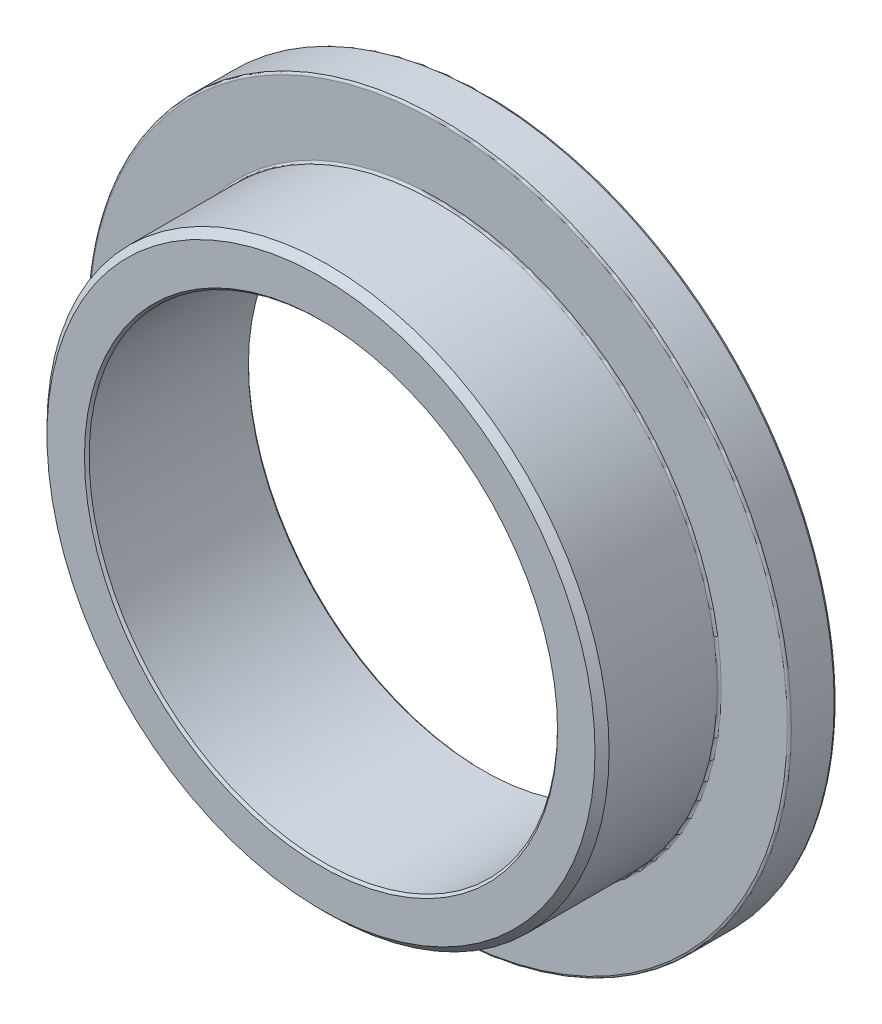
SolidWorks part; units mm, degrees
ref_plane "Front Plane" through (0, 0, 0) normal (0, 0, 1) x (1, 0, 0)
ref_plane "Top Plane" through (0, 0, 0) normal (0, 1, 0) x (1, 0, 0)
ref_plane "Right Plane" through (0, 0, 0) normal (1, 0, 0) x (0, 0, -1)
sketch "Sketch1" plane through (0, 0, 0) normal (0, 0, 1) x (1, 0, 0)
  circle A0 centre (0, 0) radius 5 construction
  circle A1 centre (0, 0) radius 6 construction
  circle A2 centre (0, 0) radius 7.5 construction
  point P5 (0, 7.5)
  dimension "ID" = 10
  dimension "OD" = 12
  dimension "Flange OD" = 15
sketch "Sketch2" plane through (0, 0, 0) normal (1, 0, 0) x (0, 0, -1)
  line L0 (-1.75, 0) -> (1.75, 0) construction
  line L1 (-1.75, 6) -> (-1.75, -6) construction
  line L2 (0, 6) -> (0, -6) construction
  line L3 (1.75, 7.5) -> (1.75, -7.5) construction
  line L4 (0, 7.5) -> (0, -7.5) construction
  line L5 (1.75, -7.5) -> (0.75, -7.5) construction
  dimension "Length" = 3.5
  dimension "Flange Thickness" = 1
sketch "Sketch3" plane through (0, 0, 0) normal (1, 0, 0) x (0, 0, -1)
  line L0 (1.75, -7.5) -> (0.75, -7.5)
  line L1 (0.75, -7.5) -> (0.75, -6)
  line L2 (0.75, -6) -> (-1.75, -6)
  line L3 (-1.75, -6) -> (-1.75, -5)
  line L4 (-1.75, 6) -> (-1.75, -6) construction
  line L5 (-1.75, -5) -> (1.75, -5)
  line L6 (1.75, 7.5) -> (1.75, -7.5) construction
  line L7 (1.75, -5) -> (1.75, -7.5)
  line L9 (0, 5) -> (0, -5) construction
  point P15 (0, -5)
revolve "Revolve1" add sketch "Sketch3" angle 360 about L0
chamfer "Chamfer1" distance 0.15 angle 45 1 edges at (6, 0, 1.75)
chamfer "Chamfer2" distance 0.05 angle 45 2 edges at (5, 0, -1.75) (5, 0, 1.75)
fillet "Fillet1" radius 0.045 3 edges at (7.5, 0, -1.75) (6, 0, -0.75) (7.5, 0, -0.75)
equation "\"D1@Chamfer1\"=(\"OD@Sketch1\"-\"ID@Sketch1\")*0.075"
equation "\"D1@Chamfer2\"=(\"OD@Sketch1\"-\"ID@Sketch1\")*0.025"
equation "\"D1@Fillet1\"=(\"Flange OD@Sketch1\"-\"OD@Sketch1\")*0.015"
